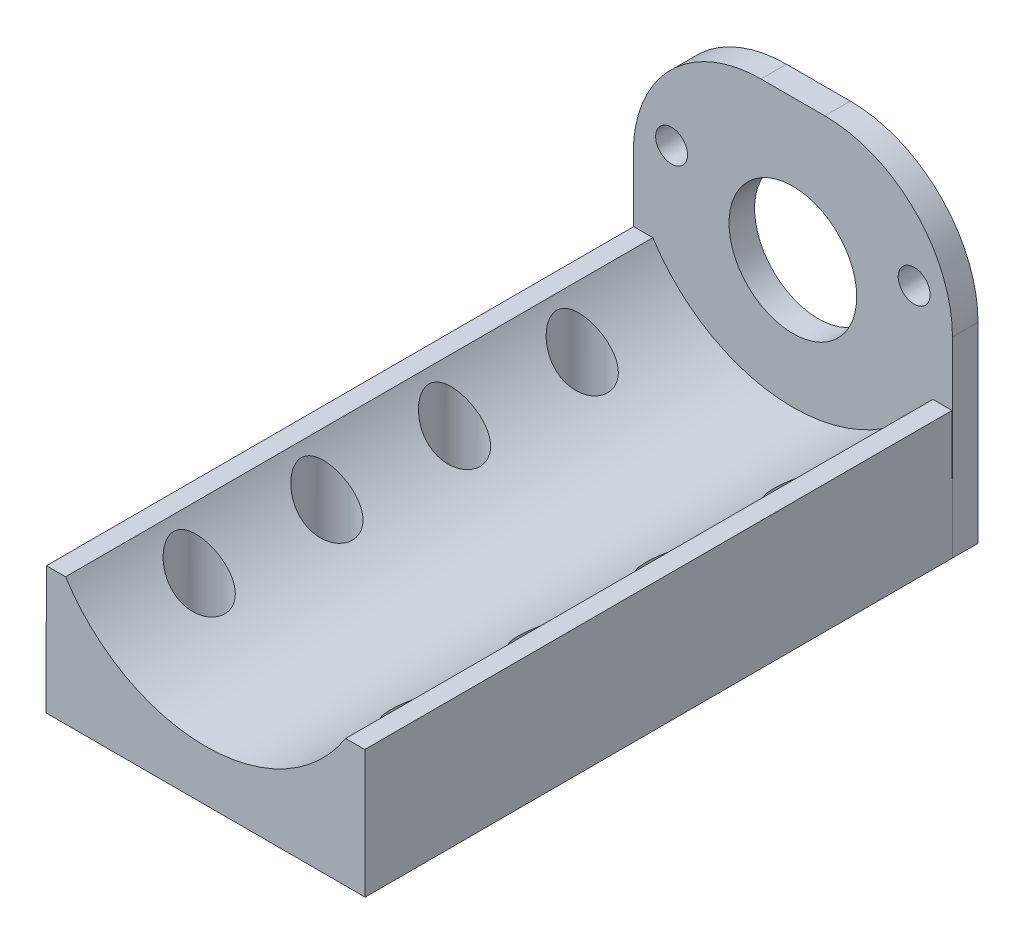
SolidWorks part; units mm, degrees
ref_plane "Front Plane" through (0, 0, 0) normal (0, 0, 1) x (1, 0, 0)
ref_plane "Top Plane" through (0, 0, 0) normal (0, 1, 0) x (1, 0, 0)
ref_plane "Right Plane" through (0, 0, 0) normal (1, 0, 0) x (0, 0, -1)
sketch "Sketch2" plane through (0, 0, 0) normal (0, 0, 1) x (1, 0, 0)
  line L0 (0, 0) -> (0, -3.978) construction
  line L3 (-12.5, -3.978) -> (12.5, -3.978)
  line L5 (6.8984, 1.9813) -> (12.5, -3.978) construction
  line L6 (-12.5, -3.978) -> (-6.8984, 1.9813) construction
  line L7 (-12.4684, 6.0219) -> (-10.9684, 6.0219)
  line L8 (-10.9684, 6.0219) -> (10.9684, 6.0219) construction
  line L9 (-12.4684, 6.0219) -> (-12.5, -3.978)
  line L10 (10.9684, 6.0219) -> (12.4684, 6.0219)
  line L11 (12.4684, 6.0219) -> (12.5, -3.978)
  arc A0 (-10.9684, 6.0219) -> (10.9684, 6.0219) centre (0, 13) ccw
  dimension "D2" = 26
  dimension "D1" = 25
  dimension "D3" = 10
  dimension "D4" = 1.5
  dimension "D5" = 1.5
extrude "Boss-Extrude1" add sketch "Sketch2" along normal blind 46
sketch "Sketch3" plane through (0, 0, 0) normal (0, 0, -1) x (-1, 0, 0)
  line L1 (-12.5, -3.978) -> (12.5, -3.978)
  line L2 (-12.5, -3.978) -> (-12.5, 21.022)
  line L3 (-12.5, 21.022) -> (12.5, 21.022)
  line L4 (12.5, -3.978) -> (12.5, 21.022)
  dimension "D1" = 25
extrude "Boss-Extrude2" add sketch "Sketch3" along normal blind 2
sketch "Sketch4" plane through (0, 0, 0) normal (0, 0, 1) x (1, 0, 0)
  line L0 (0, 13) -> (-9.5, 13) construction
  line L1 (0, 13) -> (9.5, 13) construction
  line L2 (0, 13) -> (0, 10) construction
  circle A0 centre (-9.5, 13) radius 1.25
  circle A1 centre (9.5, 13) radius 1.25
  circle A2 centre (0, 10) radius 5
  dimension "D4" = 10
  dimension "D5" = 2.5
  dimension "D6" = 2.5
  dimension "D1" = 9.5
  dimension "D2" = 9.5
  dimension "D3" = 3
extrude "Cut-Extrude1" cut sketch "Sketch4" against normal through all
fillet "Fillet1" radius 10 2 edges at (-12.5, 21.022, -1) (12.5, 21.022, -1)
sketch "Sketch5" plane through (0, -3.978, 0) normal (0, -1, 0) x (1, 0, 0)
  line L0 (-12.5, 46) -> (-12.5, 0) construction
  line L1 (12.5, -2) -> (-12.5, -2) construction
  circle A0 centre (-8.5, 8) radius 2
  dimension "D1" = 4
  dimension "D3" = 4
  dimension "D2" = 10
extrude "Cut-Extrude2" cut sketch "Sketch5" against normal through all
mirror "Mirror1" about plane through (0, 0, 0) normal (1, 0, 0) of "Cut-Extrude2"
pattern_linear "LPattern1" count 4 spacing 10 along (0, 0, 1) of "Mirror1", "Cut-Extrude2"
